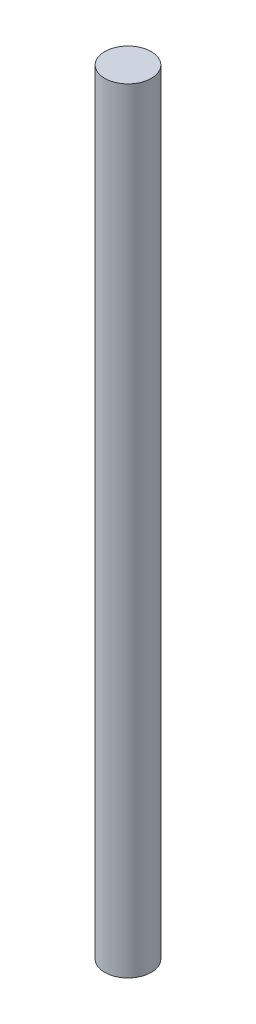
SolidWorks part; units mm, degrees
material "AISI 1020 Steel, Cold Rolled"
ref_plane "Front Plane" through (0, 0, 0) normal (0, 0, 1) x (1, 0, 0)
ref_plane "Top Plane" through (0, 0, 0) normal (0, 1, 0) x (1, 0, 0)
ref_plane "Right Plane" through (0, 0, 0) normal (1, 0, 0) x (0, 0, -1)
sketch "Sketch2" plane through (0, 0, 0) normal (0, 1, 0) x (1, 0, 0)
  circle A0 centre (0, 0) radius 7.62
  dimension "D1" = 15.24
extrude "Boss-Extrude2" add sketch "Sketch2" along normal blind 254
sketch "Sketch1" plane through (0, 0, 0) normal (1, 0, 0) x (0, 0, -1)
  circle A0 centre (0, 0) radius 7.62
  dimension "D1" = 15.24
sketch "Sketch3" plane through (0, 0, 0) normal (1, 0, 0) x (0, 0, -1)
  line L0 (0, 119.4371) -> (0, 81.3371) construction
  line L1 (0, 119.4371) -> (0, 157.5371) construction
  circle A0 centre (0, 157.5371) radius 5.08
  circle A1 centre (0, 81.3371) radius 5.08
  dimension "D1" = 38.1
  dimension "D2" = 38.1
extrude "Cut-Extrude1" cut sketch "Sketch3" against normal through all
